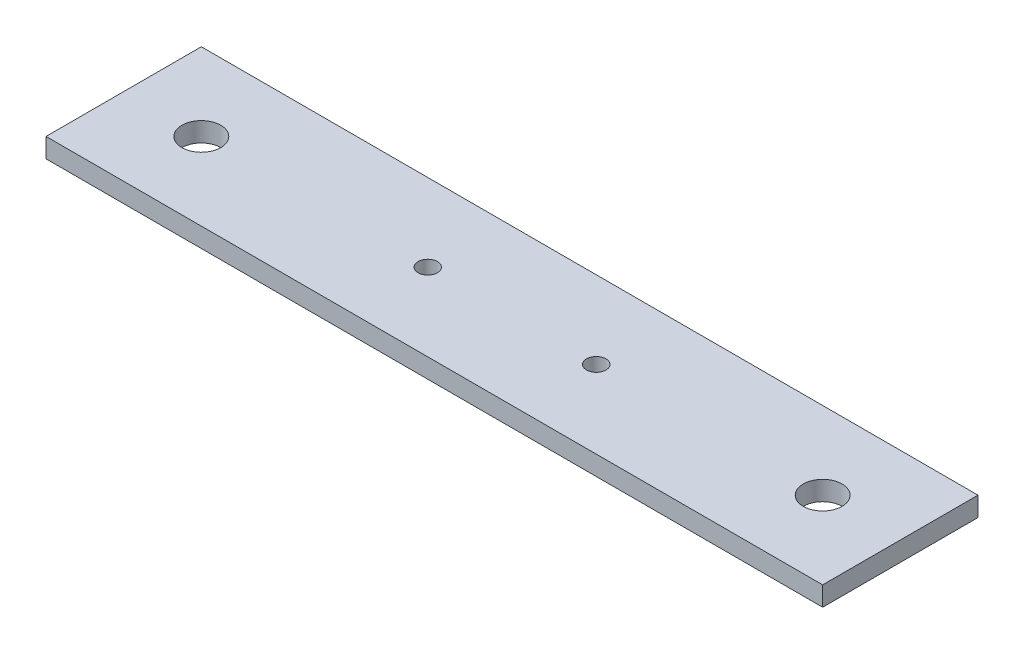
SolidWorks part; units mm, degrees
material "6061-T6 (SS)"
ref_plane "Front Plane" through (0, 0, 0) normal (0, 0, 1) x (1, 0, 0)
ref_plane "Top Plane" through (0, 0, 0) normal (0, 1, 0) x (1, 0, 0)
ref_plane "Right Plane" through (0, 0, 0) normal (1, 0, 0) x (0, 0, -1)
sketch "Sketch1" plane through (0, 0, 0) normal (0, 1, 0) x (1, 0, 0)
  line L0 (-50.8, 0) -> (50.8, 0) construction
  line L1 (63.5, -12.7) -> (-63.5, -12.7)
  line L2 (63.5, -12.7) -> (63.5, 12.7)
  line L3 (63.5, 12.7) -> (-63.5, 12.7)
  line L4 (-63.5, -12.7) -> (-63.5, 12.7)
  line L5 (63.5, -12.7) -> (-63.5, 12.7) construction
  line L6 (63.5, 12.7) -> (-63.5, -12.7) construction
  line L7 (0, 0) -> (0, 7.2774) construction
  circle A0 centre (-50.8, 0) radius 3.175
  circle A1 centre (50.8, 0) radius 3.175
  circle A2 centre (-13.7748, 0) radius 1.5875
  circle A3 centre (13.7748, 0) radius 1.5875
  point P0 (0, 0)
  dimension "D3" = 6.35
  dimension "D6" = 3.175
  dimension "D1" = 25.4
  dimension "D2" = 127
  dimension "D4" = 12.7
  dimension "D5" = 27.5496
extrude "Boss-Extrude1" add sketch "Sketch1" along normal blind 3.175
